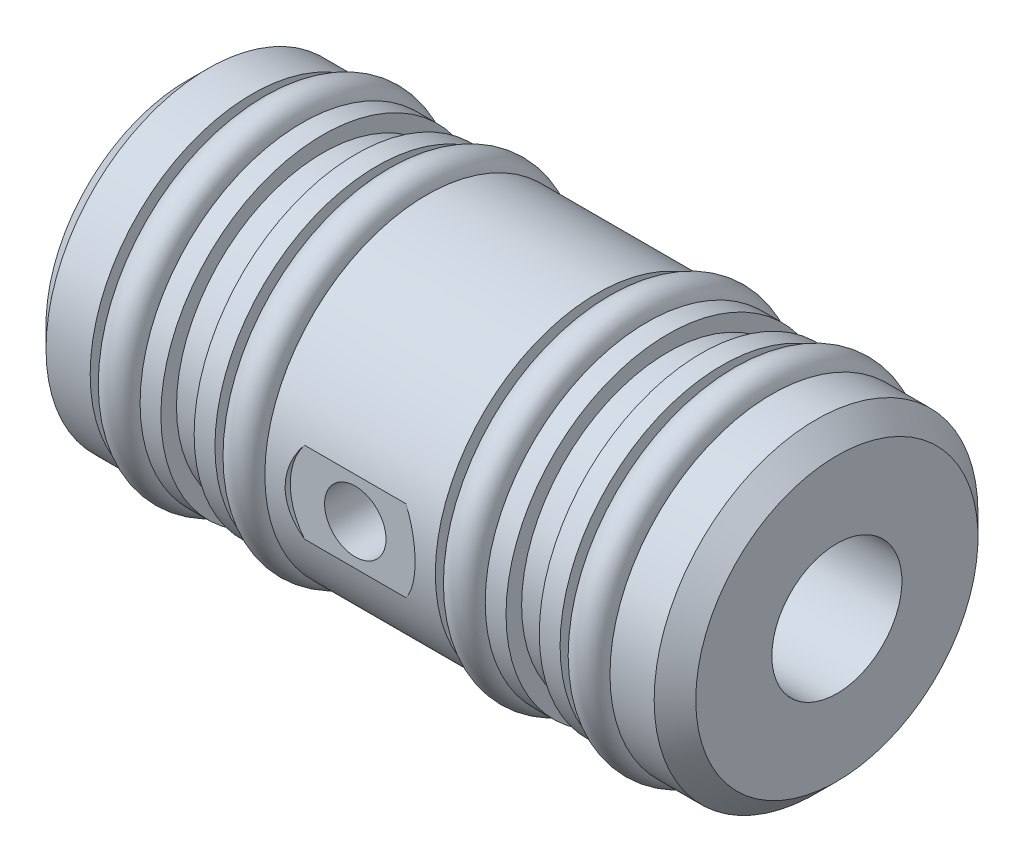
SolidWorks part; units mm, degrees
ref_plane "Front Plane" through (0, 0, 0) normal (0, 0, 1) x (1, 0, 0)
ref_plane "Top Plane" through (0, 0, 0) normal (0, 1, 0) x (1, 0, 0)
ref_plane "Right Plane" through (0, 0, 0) normal (1, 0, 0) x (0, 0, -1)
sketch "Sketch1" plane through (0, 0, 0) normal (0, 0, 1) x (1, 0, 0)
  line L0 (0, 3.1775) -> (31.75, 3.1775)
  line L1 (31.75, 3.1775) -> (31.75, 7.9121)
  line L2 (31.75, 7.9121) -> (28.575, 7.9121)
  line L3 (28.575, 7.9121) -> (28.575, 6.6675)
  line L4 (28.575, 6.6675) -> (26.1366, 6.6675)
  line L5 (26.1366, 6.6675) -> (26.1366, 7.9121)
  line L6 (26.1366, 7.9121) -> (25.1206, 7.9121)
  line L7 (25.1206, 7.9121) -> (25.1206, 7.1501)
  line L8 (0, 3.1775) -> (0, 7.9121)
  line L9 (0, 7.9121) -> (3.175, 7.9121)
  line L10 (3.175, 7.9121) -> (3.175, 6.6675)
  line L11 (3.175, 6.6675) -> (5.6134, 6.6675)
  line L12 (5.6134, 6.6675) -> (5.6134, 7.9121)
  line L13 (5.6134, 7.9121) -> (6.6294, 7.9121)
  line L14 (6.6294, 7.9121) -> (6.6294, 7.1501)
  line L15 (6.6294, 7.1501) -> (8.255, 7.1501)
  line L16 (8.255, 7.1501) -> (8.255, 7.9121)
  line L17 (8.255, 7.9121) -> (9.271, 7.9121)
  line L18 (9.271, 7.9121) -> (9.271, 6.6675)
  line L19 (9.271, 6.6675) -> (11.7094, 6.6675)
  line L20 (11.7094, 6.6675) -> (11.7094, 7.9121)
  line L21 (11.7094, 7.9121) -> (20.0406, 7.9121)
  line L22 (20.0406, 7.9121) -> (20.0406, 6.6675)
  line L23 (25.1206, 7.1501) -> (23.495, 7.1501)
  line L24 (23.495, 7.1501) -> (23.495, 7.9121)
  line L25 (23.495, 7.9121) -> (22.479, 7.9121)
  line L26 (22.479, 7.9121) -> (22.479, 6.6675)
  line L27 (22.479, 6.6675) -> (20.0406, 6.6675)
  line L28 (0, 0) -> (31.75, 0) construction
  dimension "D1" = 1.016
  dimension "D2" = 1.6256
  dimension "OAL" = 31.75
  dimension "D3" = 1.016
  dimension "D4" = 3.1775
  dimension "O-ring groove width" = 2.4384
  dimension "D5" = 6.6675
  dimension "Edge to 1st o-ring groove" = 3.175
  dimension "D6" = 7.1501
  dimension "D7" = 7.9121
  dimension "D8" = 2.4384
  dimension "D9" = 2.4384
  dimension "D10" = 1.016
  dimension "Edge to 3rd o-ring groove" = 20.0406
  dimension "D11" = 1.6256
  dimension "D12" = 1.016
  dimension "D13" = 2.4384
revolve "Revolve1" add sketch "Sketch1" angle 360 about L28
chamfer "Chamfer1" distance 1.016 angle 45 2 edges at (0, 0, 7.9121) (31.75, 0, 7.9121)
ref_plane "Plane1" through (0, 0, -7.9121) normal (0, 0, 1) x (1, 0, 0)
hole_wizard "1/4 (0.25) Diameter Hole1" positions "3DSketch1" profile "Sketch2" hole size "1/4" standard "Ansi Inch"
sketch3d "3DSketch1"
  point P0 (15.875, 0, 7.9121)
  dimension "Edge to air hole" = 15.875
sketch "Sketch2" plane through (15.875, 0, 7.9121) normal (1, 0, 0) x (0, -1, 0)
  line L0 (0, 0) -> (0, 0.254)
  line L1 (0, 0.254) -> (3.175, 0.254)
  line L2 (3.175, 0.254) -> (3.175, 0)
  line L5 (3.175, 0) -> (0, 0)
  line L10 (0, 0.254) -> (-3.175, 0.254) construction
  line L11 (0, -6.35) -> (0, 107.95) construction
  dimension "Hole Dia." = 6.35
  dimension "Hole Depth" = 0.254
  dimension "Drill Angle" = 180
hole_wizard "Air Hole" positions "Sketch4" profile "Sketch3" tap size "M3x0.5" standard "Ansi Metric"
sketch "Sketch4" plane through (0, 0, 7.6581) normal (0, 0, 1) x (1, 0, 0)
  circle A0 centre (15.875, 0) radius 3.175 construction
  point P0 (15.875, 0)
sketch "Sketch3" plane through (15.875, 0, 7.6581) normal (1, 0, 0) x (0, -1, 0)
  line L0 (0, 0) -> (0, 7.0978)
  line L1 (0, 7.0978) -> (1.2446, 6.35)
  line L2 (1.2446, 6.35) -> (1.2446, 6.096)
  line L3 (1.2446, 6.096) -> (1.5, 6.096)
  line L4 (1.5, 6.096) -> (1.5, 0)
  line L5 (1.5, 0) -> (0, 0)
  line L10 (0, 7.0978) -> (-1.2446, 6.35) construction
  line L11 (0, -6.35) -> (0, 107.95) construction
  dimension "Tap Drill Dia." = 2.4892
  dimension "Tap Drill Depth" = 6.35
  dimension "Thread Major Dia." = 3
  dimension "Thread Depth" = 6.096
  dimension "Drill Angle" = 118
sketch "Sketch5" plane through (0, 0, 0) normal (0, 0, 1) x (1, 0, 0)
  line L3 (5.6134, 7.9121) -> (5.6134, -7.9121) construction
  line L4 (11.7094, 7.9121) -> (11.7094, -7.9121) construction
  line L5 (20.0406, -7.9121) -> (20.0406, 7.9121) construction
  line L6 (26.1366, -7.9121) -> (26.1366, 7.9121) construction
  line L7 (0, 0) -> (51.7691, 0) construction
  circle A0 centre (27.3566, 7.5235) radius 0.8585
  circle A1 centre (21.2606, 7.5235) radius 0.8585
  circle A2 centre (10.4894, 7.5235) radius 0.8585
  circle A3 centre (4.3942, 7.5235) radius 0.8585
  dimension "D1" = 1.717
  dimension "D2" = 8.382
  dimension "D6" = 1.22
  dimension "D3" = 1.2192
  dimension "D4" = 1.22
  dimension "D5" = 1.22
revolve "Revolve2" add sketch "Sketch5" angle 360 about L7
